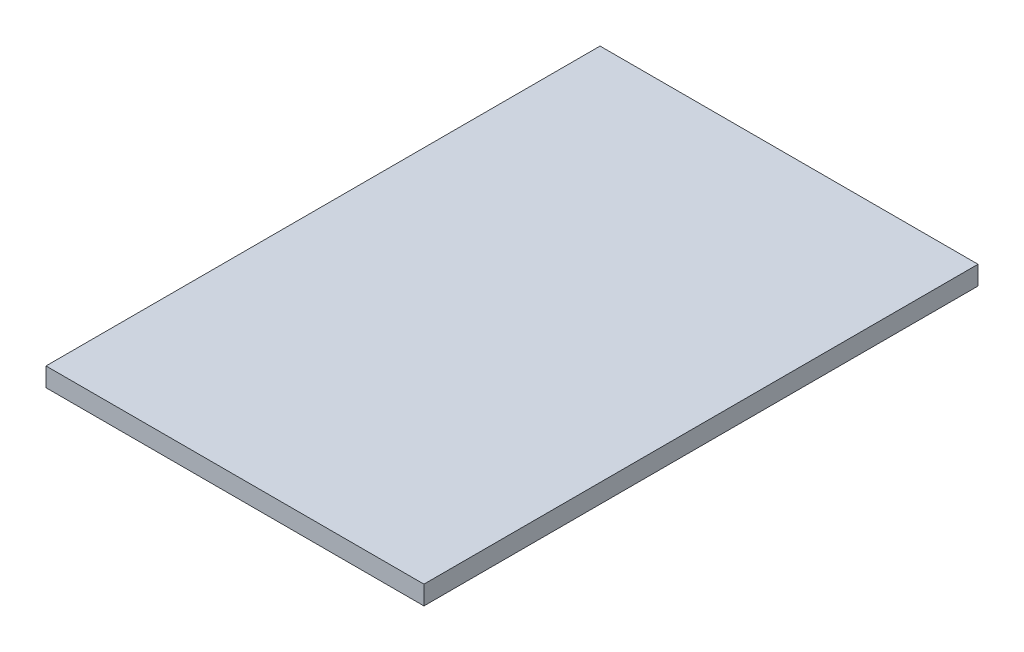
SolidWorks part; units mm, degrees
ref_plane "Front Plane" through (0, 0, 0) normal (0, 0, 1) x (1, 0, 0)
ref_plane "Top Plane" through (0, 0, 0) normal (0, 1, 0) x (1, 0, 0)
ref_plane "Right Plane" through (0, 0, 0) normal (1, 0, 0) x (0, 0, -1)
sketch "Sketch1" plane through (0, 0, 0) normal (0, 1, 0) x (1, 0, 0)
  line L1 (-63.5, 93.091) -> (63.5, 93.091)
  line L2 (-63.5, 93.091) -> (-63.5, -93.091)
  line L3 (-63.5, -93.091) -> (63.5, -93.091)
  line L4 (63.5, 93.091) -> (63.5, -93.091)
  line L5 (-63.5, 93.091) -> (63.5, -93.091) construction
  line L6 (-63.5, -93.091) -> (63.5, 93.091) construction
  point P0 (0, 0)
  dimension "D1" = 127
  dimension "D2" = 186.182
extrude "Boss-Extrude1" add sketch "Sketch1" along normal blind 6.35
